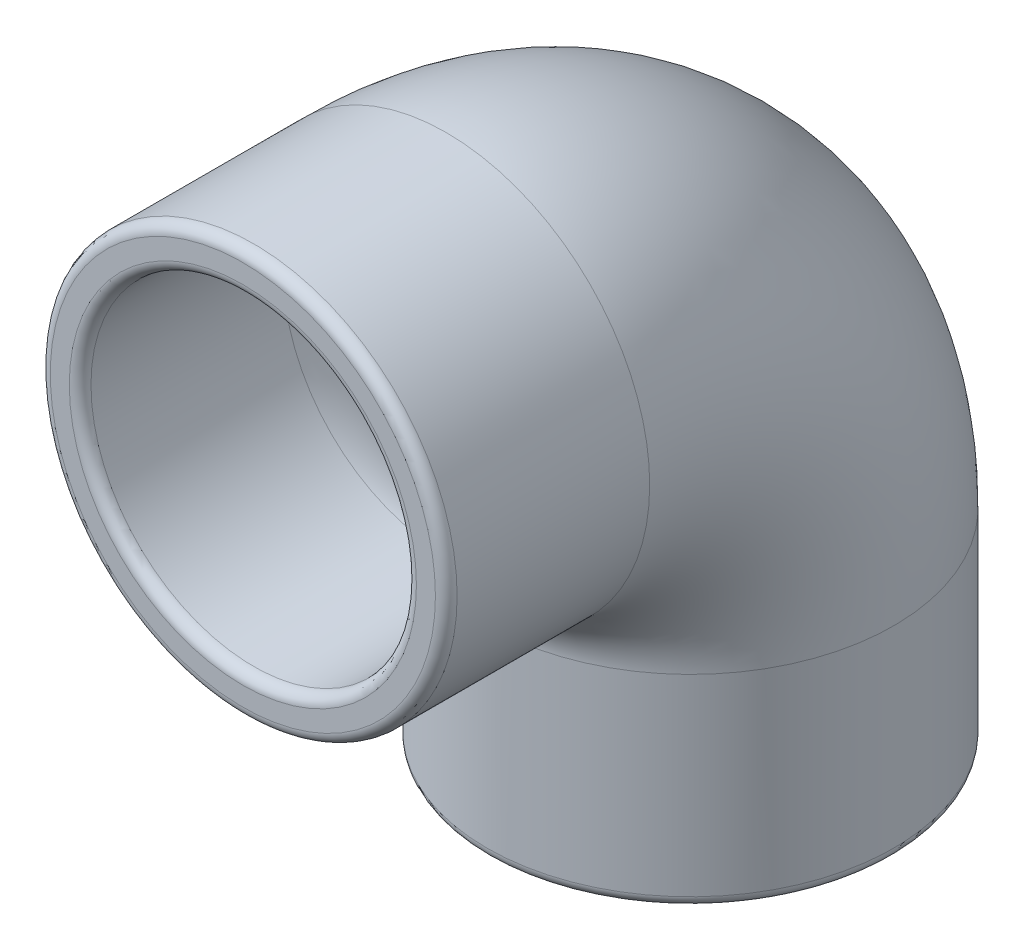
SolidWorks part; units mm, degrees
ref_plane "Front Plane" through (0, 0, 0) normal (0, 0, 1) x (1, 0, 0)
ref_plane "Top Plane" through (0, 0, 0) normal (0, 1, 0) x (1, 0, 0)
ref_plane "Right Plane" through (0, 0, 0) normal (1, 0, 0) x (0, 0, -1)
sketch "Sketch1" plane through (0, 0, 0) normal (0, 0, 1) x (1, 0, 0)
  circle A0 centre (0, 0) radius 12
  circle A1 centre (0, 0) radius 15
  dimension "D1" = 24
  dimension "D2" = 30
sketch "Sketch2" plane through (0, 0, 0) normal (1, 0, 0) x (0, 0, -1)
  line L0 (0, 0) -> (15, 0)
  line L1 (33, -18) -> (33, -33)
  arc A0 (33, -18) -> (15, 0) centre (15, -18) ccw
  dimension "D1" = 18
sweep "Sweep3" add profiles "Sketch1" path "Sketch2"
fillet "Fillet4" radius 0.8 2 edges at (15, 0, 0) (12, 0, 0)
fillet "Fillet5" radius 0.8 2 edges at (15, -33, -33) (12, -33, -33)
sketch "Sketch3" plane through (0, 0, 0) normal (1, 0, 0) x (0, 0, -1)
  line L0 (33, -64.7443) -> (33, 0) construction
  line L1 (33, 0) -> (-20.736, 0) construction
